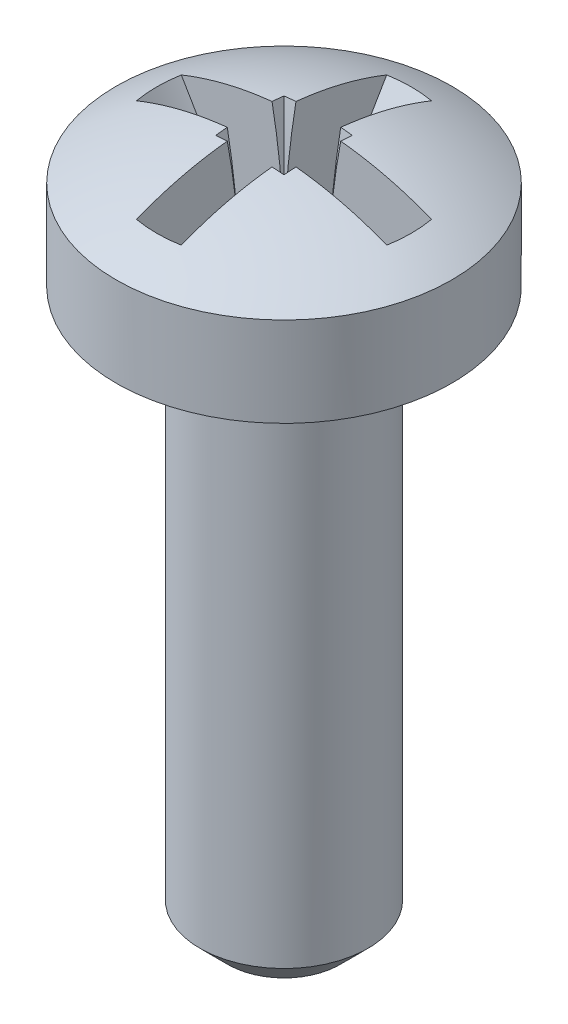
SolidWorks part; units mm, degrees
material "Acier non allié"
ref_plane "Plan de face" through (0, 0, 0) normal (0, 0, 1) x (1, 0, 0)
ref_plane "Plan de dessus" through (0, 0, 0) normal (0, 1, 0) x (1, 0, 0)
ref_plane "Plan de droite" through (0, 0, 0) normal (1, 0, 0) x (0, 0, -1)
sketch "Esquisse1" plane through (0, 0, 0) normal (0, 0, 1) x (1, 0, 0)
  line L0 (0, 0) -> (-1, 0)
  line L1 (-1.5, 0.5) -> (-1.5, 10)
  line L2 (-1.5, 10) -> (-3, 10)
  line L3 (-3, 10) -> (-3, 11.6)
  line L4 (0, 0) -> (0, -0.8642) construction
  line L5 (0, 12.4) -> (0, 0)
  line L6 (-1, 0) -> (-1.5, 0.5)
  line L7 (0, 0) -> (0, 12.4) construction
  arc A1 (0, 12.4) -> (-3, 11.6) centre (0, 6.375) ccw
  point P1 (-1.5, 0)
  dimension "D1" = 0.8
  dimension "D3" = 0.5
  dimension "D2" = 0.5
revolve "Révolution1" add sketch "Esquisse1" angle 360 about L5
sketch "Esquisse3" plane through (0, 0, 0) normal (0, 0, 1) x (1, 0, 0)
  line L1 (-1.5, 9.5) -> (1.5, 9.5)
  line L5 (0, 12.4) -> (0, 0) construction
  point P4 (0, 9.5)
split line "Ligne de séparation16"
sketch "Esquisse4" plane through (0, 0, 0) normal (0, 0, 1) x (1, 0, 0)
  line L0 (0, 20.1) -> (-3, 20.1)
  line L1 (0, 12.4) -> (0, 0) construction
  line L2 (-3, 13.2177) -> (-1.2, 10.1)
  line L3 (-1.2, 10.1) -> (0, 10.1)
  line L4 (0, 9.5) -> (0, 10) construction
  line L5 (0, 10.1) -> (0, 20.1)
  line L6 (-3, 13.2177) -> (-3, 20.1)
  dimension "D1" = 3
  dimension "D2" = 120
  dimension "D3" = 10
revolve "Révolution2" add sketch "Esquisse4" angle 360 about L5
sketch "Esquisse5" plane through (0, 10.1, 0) normal (0, -1, 0) x (1, 0, 0)
  line L0 (-12.4, -0.4) -> (-12.4, -4.4)
  line L1 (-0.4, 0.4) -> (-12.4, 0.4)
  line L2 (-0.4, 0.4) -> (-0.4, 4.4)
  line L3 (-0.4, 4.4) -> (-12.4, 4.4)
  line L4 (-12.4, 0.4) -> (-12.4, 4.4)
  line L5 (-0.4, 0) -> (0, 0) construction
  line L6 (-0.4, -4.4) -> (-12.4, -4.4)
  line L7 (-0.4, -0.4) -> (-0.4, -4.4)
  line L8 (-0.4, -0.4) -> (-12.4, -0.4)
  dimension "D1" = 12
  dimension "D3" = 0.4
  dimension "D2" = 4
revolve "Enlèvement de matière-Révolution2" cut sketch "Esquisse5" angle 360 about L4
pattern_circular "Répétition circulaire1" count 4 over 360 about axis through (0, 0, 0) along (0, 1, 0) of "Enlèvement de matière-Révolution2"
combine bodies "Combiner1" operation type subtract main body 101 bodies to subtract 108
equation "\"D1@Esquisse1\" = \"F\"/3"
equation "\"D2@Esquisse1\" = \"D\"/6"
equation "\"D3@Esquisse1\" = \"D\"/6"
equation "\"D3@Esquisse5\" = \"NL\"/2"
